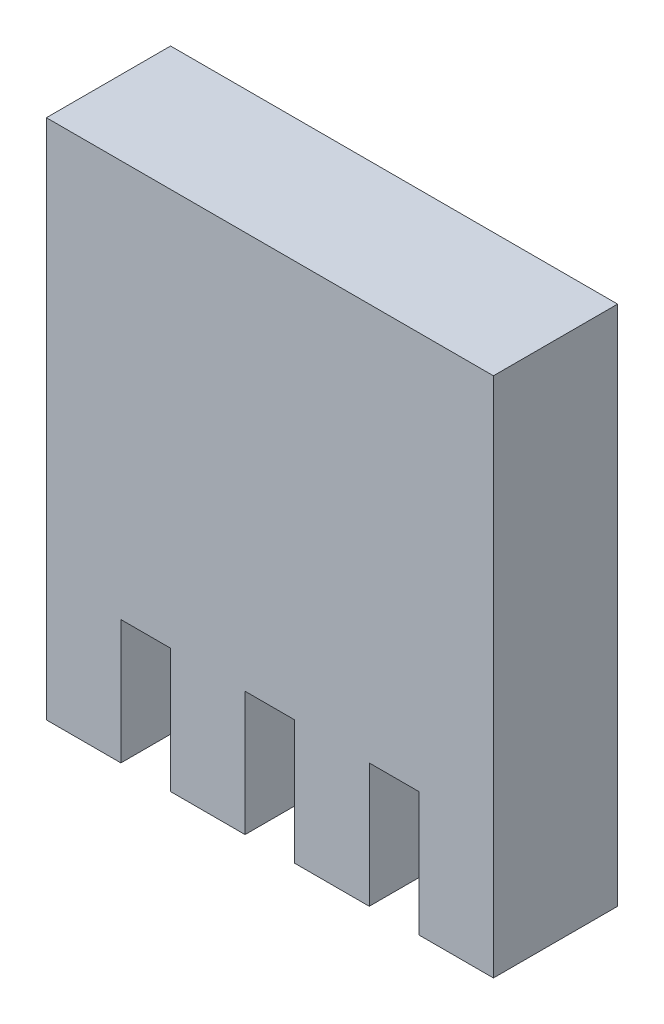
SolidWorks part; units mm, degrees
ref_plane "Plan de face" through (0, 0, 0) normal (0, 0, 1) x (1, 0, 0)
ref_plane "Plan de dessus" through (0, 0, 0) normal (0, 1, 0) x (1, 0, 0)
ref_plane "Plan de droite" through (0, 0, 0) normal (1, 0, 0) x (0, 0, -1)
sketch "Esquisse1" plane through (0, 0, 0) normal (0, 0, 1) x (1, 0, 0)
  line L1 (0, 0) -> (18, 0)
  line L2 (0, 0) -> (0, 16)
  line L3 (0, 16) -> (18, 16)
  line L4 (18, 0) -> (18, 16)
  line L5 (0, 0) -> (3, 0)
  line L6 (0, 0) -> (0, -5)
  line L7 (0, -5) -> (3, -5)
  line L8 (3, 0) -> (3, -5)
  line L9 (10, -5) -> (13, -5)
  line L10 (10, -5) -> (10, 0)
  line L11 (10, 0) -> (13, 0)
  line L12 (13, -5) -> (13, 0)
  line L13 (15, -5) -> (18, -5)
  line L14 (15, -5) -> (15, 0)
  line L15 (15, 0) -> (18, 0)
  line L16 (18, -5) -> (18, 0)
  line L17 (5, 0) -> (8, 0)
  line L18 (5, 0) -> (5, -5)
  line L19 (5, -5) -> (8, -5)
  line L20 (8, 0) -> (8, -5)
  dimension "D1" = 16
  dimension "D2" = 18
  dimension "D3" = 5
  dimension "D4" = 3
  dimension "D5" = 3
  dimension "D6" = 3
  dimension "D7" = 5
  dimension "D8" = 5
  dimension "D9" = 2
  dimension "D10" = 5
  dimension "D11" = 3
  dimension "D12" = 2
extrude "Boss.-Extru.2" add sketch "Esquisse1" along normal blind 5 contours L1 L4 L3 L2 | L8 L1 L6 L7 | L9 L12 L1 L10 | L13 L16 L1 L14 | L18 L19 L20 L17
